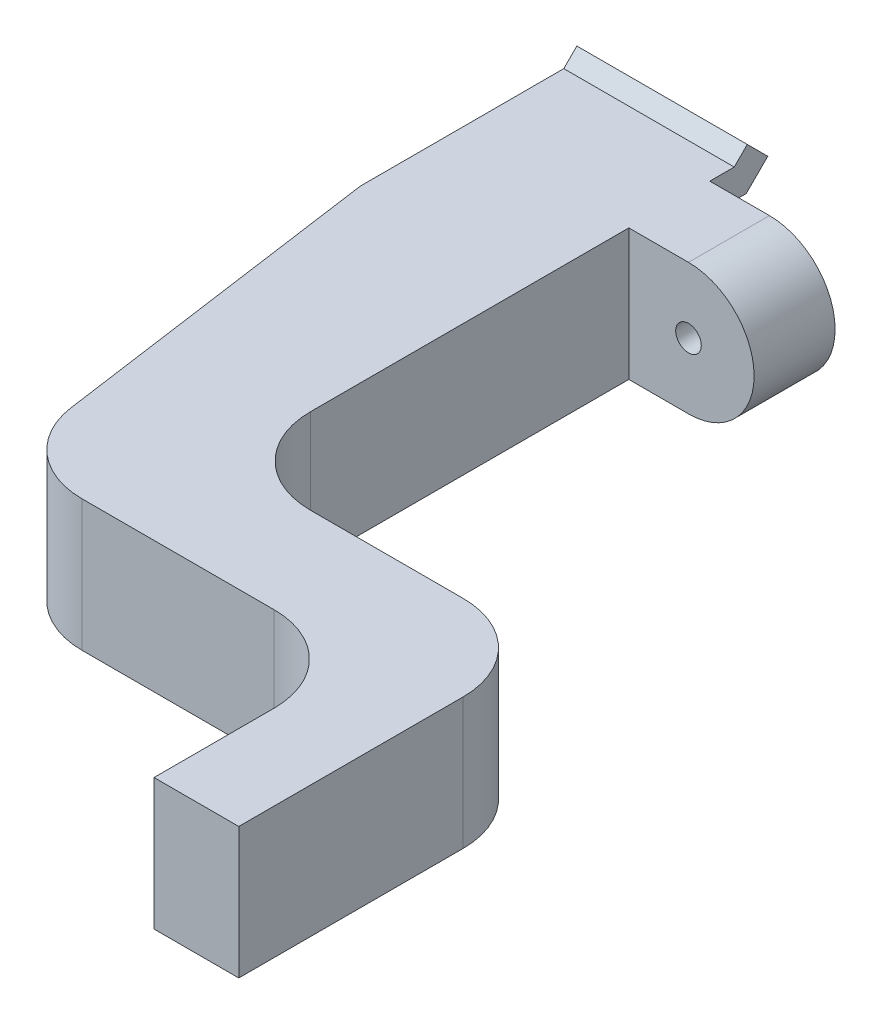
SolidWorks part; units mm, degrees
ref_plane "Front Plane" through (0, 0, 0) normal (0, 0, 1) x (1, 0, 0)
ref_plane "Top Plane" through (0, 0, 0) normal (0, 1, 0) x (1, 0, 0)
ref_plane "Right Plane" through (0, 0, 0) normal (1, 0, 0) x (0, 0, -1)
sketch "Sketch2" plane through (0, 0, 0) normal (0, 0, 1) x (1, 0, 0)
  line L0 (0, 5.9203) -> (0, 8.9503) construction
  line L1 (-5, -5.8182) -> (5, -5.8182)
  line L2 (-5, -5.8182) -> (-5, 8.9503)
  line L3 (-5, 8.9503) -> (5, 8.9503)
  line L4 (5, -5.8182) -> (5, 8.9503)
  line L5 (-26.3166, 8.9503) -> (11.3834, 8.9503) construction
  line L7 (5.6834, 5.9203) -> (-25.9417, 5.9203) construction
  line L8 (0, -5.8182) -> (0, -2.7882) construction
  point P0 (0, 0)
  dimension "D1" = 10
extrude "Boss-Extrude1" add sketch "Sketch2" along normal blind 5
sketch "Sketch8" plane through (-5, 0, 0) normal (-1, 0, 0) x (0, 0, 1)
  line L6 (-0.15, 5.7703) -> (0, 5.7703)
  line L7 (0, 8.9503) -> (0, -5.8182) construction
  line L8 (0, 5.7703) -> (0, 4.0703)
  line L9 (0, 4.0703) -> (-0.15, 4.0703)
  line L11 (-0.15, -1.9297) -> (0, -1.9297)
  line L12 (-2.1379, 4.0703) -> (-0.15, 4.0703)
  line L13 (-0.15, 4.0703) -> (-0.15, 5.7703)
  line L14 (-0.15, 5.7703) -> (-1.4337, 5.7703)
  line L15 (-1.4337, 5.7703) -> (-2.2, 6.5366)
  line L16 (-2.2, 6.5366) -> (-3.4021, 5.3345)
  line L17 (-3.4021, 5.3345) -> (-2.1379, 4.0703)
  line L18 (-2.1379, 4.0703) -> (-0.15, 4.0703)
  line L20 (-0.15, 5.7703) -> (-1.4337, 5.7703)
  line L21 (-1.4337, 5.7703) -> (-2.2, 6.5366)
  line L22 (-2.2, 6.5366) -> (-3.4021, 5.3345)
  line L23 (-3.4021, 5.3345) -> (-2.1379, 4.0703)
  line L24 (-2.1379, -1.9297) -> (-0.15, -1.9297)
  line L25 (-0.15, -1.9297) -> (-0.15, -0.2297)
  line L26 (-0.15, -0.2297) -> (-1.4337, -0.2297)
  line L27 (-1.4337, -0.2297) -> (-2.2, 0.5366)
  line L28 (-2.2, 0.5366) -> (-3.4021, -0.6655)
  line L29 (-3.4021, -0.6655) -> (-2.1379, -1.9297)
  line L30 (-2.1379, -1.9297) -> (-0.15, -1.9297)
  line L32 (-0.15, -0.2297) -> (-1.4337, -0.2297)
  line L33 (-1.4337, -0.2297) -> (-2.2, 0.5366)
  line L34 (-2.2, 0.5366) -> (-3.4021, -0.6655)
  line L35 (-3.4021, -0.6655) -> (-2.1379, -1.9297)
  line L37 (-0.15, -0.2297) -> (0, -0.2297)
  line L38 (0, -1.9297) -> (0, -0.2297)
  dimension "D1" = 0.15
  dimension "D2" = 0.15
extrude "Boss-Extrude4" add sketch "Sketch8" against normal up to surface (10 mm away) up to face at (5, 1.566, 2.5)
sketch "Sketch9" plane through (0, 0, 0) normal (0, 0, -1) x (-1, 0, 0)
  line L4 (-5, 8.9503) -> (-5, 5.7703)
  line L5 (-5, 5.7703) -> (5, 5.7703)
  line L6 (5, 5.7703) -> (5, 8.9503)
  line L7 (5, 8.9503) -> (-5, 8.9503)
  line L8 (-5, 8.9503) -> (-5, 5.7703)
  line L10 (5, 5.7703) -> (5, 8.9503)
  line L11 (5, 8.9503) -> (-5, 8.9503)
  line L16 (5, -1.9297) -> (-5, -1.9297)
  line L17 (-5, -1.9297) -> (-5, -5.8182)
  line L18 (-5, -5.8182) -> (5, -5.8182)
  line L19 (5, -5.8182) -> (5, -1.9297)
  line L21 (-5, -1.9297) -> (-5, -5.8182)
  line L22 (-5, -5.8182) -> (5, -5.8182)
  line L23 (5, -5.8182) -> (5, -1.9297)
  line L26 (-5, 5.7703) -> (5, 5.7703)
  line L27 (5, -1.9297) -> (-5, -1.9297)
  dimension "D1" = 0
  dimension "D2" = 0
extrude "Cut-Extrude3" cut sketch "Sketch9" against normal blind 5
sketch "Sketch10" plane through (0, 5.7703, 0) normal (0, 1, 0) x (1, 0, 0)
  line L0 (-5, -5) -> (-5, -10.5)
  line L1 (-5, -10.5) -> (-2.2245, -30.2484)
  line L3 (-5, -5) -> (5, -5)
  line L4 (-120.9789, 453.7107) -> (412.3545, 453.7107) construction
  line L6 (5, -5) -> (5, -14)
  line L7 (5, -14) -> (5, -23.4328)
  line L8 (10, -28.4328) -> (18.9679, -28.4328)
  line L9 (23.9679, -33.4328) -> (23.9679, -46.6007)
  line L10 (23.9679, -46.6007) -> (18.9956, -46.6007)
  line L11 (18.9956, -46.6007) -> (18.9956, -39.5525)
  line L14 (13.9956, -34.5525) -> (2.7268, -34.5525)
  arc A2 (18.9956, -39.5525) -> (13.9956, -34.5525) centre (13.9956, -39.5525) ccw
  arc A3 (18.9679, -28.4328) -> (23.9679, -33.4328) centre (18.9679, -33.4328) cw
  arc A4 (5, -23.4328) -> (10, -28.4328) centre (10, -23.4328) ccw
  arc A5 (2.7268, -34.5525) -> (-2.2245, -30.2484) centre (2.7268, -29.5525) cw
  dimension "D1" = 172
  dimension "D2" = 5
  dimension "D5" = 5.5
  dimension "D6" = 9
extrude "Boss-Extrude5" add sketch "Sketch10" against normal up to surface (7.7 mm away) up to face at (0, -1.9297, 1.4311)
ref_plane "Plane1" through (0, 0, 2.75) normal (0, 0, 1) x (1, 0, 0)
sketch "Sketch12" plane through (0, 0, 0) normal (0, 0, 1) x (1, 0, 0)
  line L0 (5, 5.7703) -> (8.5, 5.7703)
  line L1 (8.5, -1.9297) -> (5, -1.9297)
  line L2 (5, -1.9297) -> (5, 5.7703)
  line L3 (18.9956, 5.7703) -> (13.9956, 5.7703) construction
  line L4 (13.9956, -1.9297) -> (18.9956, -1.9297) construction
  line L5 (5, 5.3345) -> (5, 6.5366) construction
  line L7 (5, 6.5366) -> (5, 5.7703) construction
  arc A0 (8.5, 5.7703) -> (8.5, -1.9297) centre (8.5, 1.9203) cw
  circle A1 centre (8.5, 1.9203) radius 0.75
  dimension "D1" = 1.5
  dimension "D2" = 3.5
extrude "Boss-Extrude7" add sketch "Sketch12" along normal offset from surface (4.75 mm away) 2 up to plane "Plane1" offset beyond the face yes
